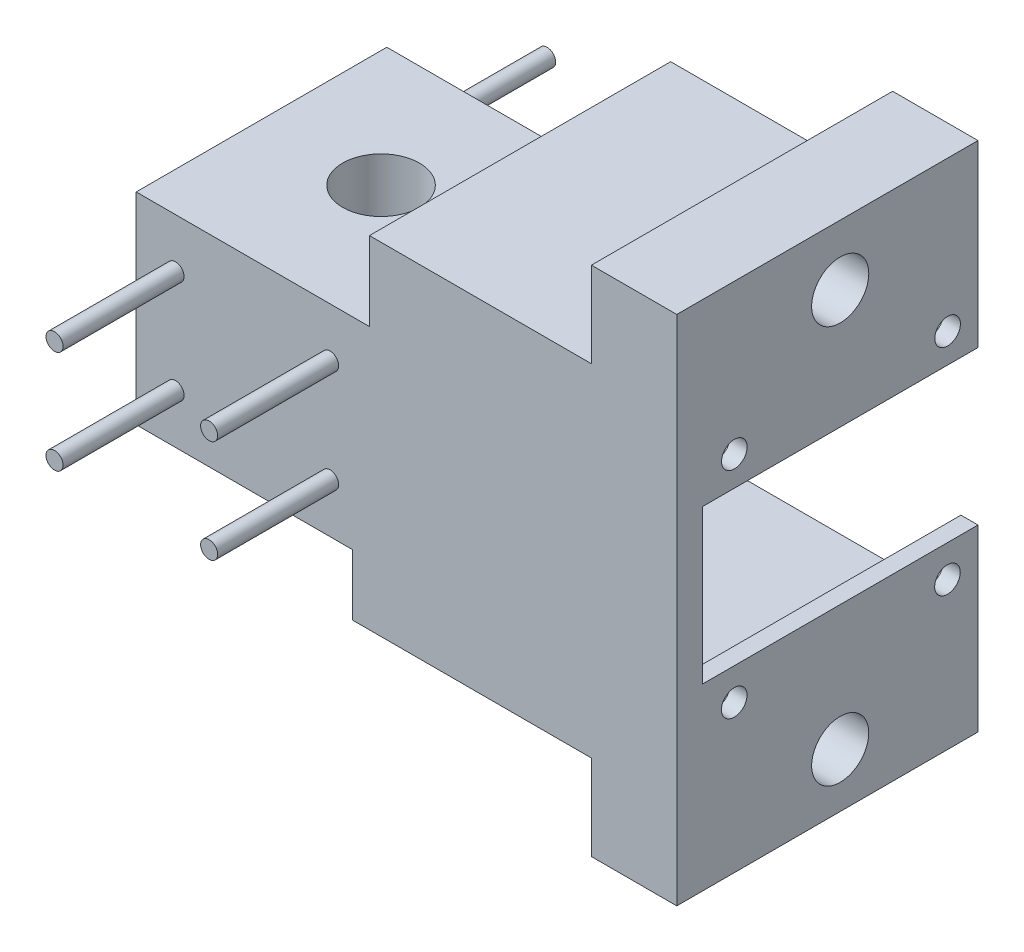
SolidWorks part; units mm, degrees
ref_plane "Front Plane" through (0, 0, 0) normal (0, 0, 1) x (1, 0, 0)
ref_plane "Top Plane" through (0, 0, 0) normal (0, 1, 0) x (1, 0, 0)
ref_plane "Right Plane" through (0, 0, 0) normal (1, 0, 0) x (0, 0, -1)
sketch "Sketch1" plane through (0, 0, -264.675) normal (0, 0, -1) x (-1, 0, 0)
  line L1 (-28.6765, -381.8964) -> (-63.3765, -381.8964)
  line L2 (-28.6765, -381.8964) -> (-28.6765, -411.8964)
  line L3 (-28.6765, -411.8964) -> (-63.3765, -411.8964)
  line L4 (-63.3765, -381.8964) -> (-63.3765, -411.8964)
extrude "Boss-Extrude1" add sketch "Sketch1" along normal up to surface (38.29 mm away)
sketch "Sketch2" plane through (0, 0, -264.675) normal (0, 0, 1) x (1, 0, 0)
  circle A0 centre (34.5265, -389.2464) radius 1.27
  circle A1 centre (34.5265, -404.5464) radius 1.27
  circle A2 centre (57.5265, -404.5464) radius 1.27
  circle A3 centre (57.5265, -389.2464) radius 1.27
  dimension "D1" = 2.54
extrude "Boss-Extrude2" add sketch "Sketch2" along a picked direction on the side of the normal blind 18 contours A0 | A3 | A2 | A1
sketch "Sketch4" plane through (0, -381.8964, 0) normal (0, 1, 0) x (1, 0, 0)
  circle A0 centre (46.0265, 283.7499) radius 5.715
  dimension "D1" = 11.43
extrude "Cut-Extrude1" cut sketch "Sketch4" against normal through all
sketch "Sketch5" plane through (0, -411.8964, 0) normal (0, -1, 0) x (1, 0, 0)
  circle A0 centre (46.4533, -275.536) radius 1.625
  circle A1 centre (54.2404, -284.1767) radius 1.625
  circle A2 centre (45.5996, -291.9638) radius 1.625
  circle A3 centre (37.8125, -283.3231) radius 1.625
  dimension "D1" = 3.25
extrude "Boss-Extrude4" add sketch "Sketch5" along normal blind 5
sketch "Sketch6" plane through (0, 0, -301.957) normal (0, 0, -1) x (-1, 0, 0)
  circle A0 centre (-57.5265, -389.2464) radius 1.27
  circle A1 centre (-34.5265, -389.2464) radius 1.27
  circle A2 centre (-34.5265, -404.5464) radius 1.27
  circle A3 centre (-57.5265, -404.5464) radius 1.27
  dimension "D1" = 2.54
extrude "Boss-Extrude5" add sketch "Sketch6" along normal up to surface (18 mm away)
sketch "Sketch8" plane through (63.3765, 0, 0) normal (1, 0, 0) x (0, 0, -1)
  line L1 (268.485, -420.9724) -> (264.675, -420.9724)
  line L2 (268.485, -420.9724) -> (268.485, -370.1724)
  line L3 (268.485, -370.1724) -> (264.675, -370.1724)
  line L4 (264.675, -420.9724) -> (264.675, -370.1724)
  line L5 (268.485, -420.9724) -> (264.675, -370.1724) construction
  line L6 (268.485, -370.1724) -> (264.675, -420.9724) construction
  point P0 (266.58, -395.5724)
  dimension "D1" = 50.8
  dimension "D2" = 3.81
extrude "Boss-Extrude6" add sketch "Sketch8" along normal blind 45.72
sketch "Sketch9" plane through (0, 0, -268.485) normal (0, 0, -1) x (-1, 0, 0)
  line L0 (-63.3765, -381.8964) -> (-63.3765, -370.1724) construction
  line L1 (-109.0965, -370.1724) -> (-63.3765, -370.1724)
  line L2 (-109.0965, -370.1724) -> (-109.0965, -372.7124)
  line L3 (-106.5565, -372.7124) -> (-63.3765, -372.7124)
  line L4 (-63.3765, -370.1724) -> (-63.3765, -372.7124)
  line L6 (-109.0965, -420.9724) -> (-63.3765, -420.9724)
  line L7 (-109.0965, -420.9724) -> (-109.0965, -418.4324)
  line L8 (-106.5565, -418.4324) -> (-63.3765, -418.4324)
  line L9 (-63.3765, -420.9724) -> (-63.3765, -418.4324)
  line L10 (-106.5565, -407.0024) -> (-106.5565, -418.4324)
  line L12 (-109.0965, -372.7124) -> (-109.0965, -384.1424)
  line L14 (-106.5565, -372.7124) -> (-106.5565, -384.1424)
  line L15 (-106.5565, -384.1424) -> (-109.0965, -384.1424)
  line L17 (-106.5565, -407.0024) -> (-109.0965, -407.0024)
  line L19 (-109.0965, -407.0024) -> (-109.0965, -418.4324)
  point P14 (-106.5565, -395.5724)
  dimension "D1" = 2.54
  dimension "D2" = 2.54
  dimension "D3" = 2.54
extrude "Boss-Extrude7" add sketch "Sketch9" along normal up to surface (41 mm away)
sketch "Sketch10" plane through (109.0965, 0, 0) normal (1, 0, 0) x (0, 0, -1)
  circle A0 centre (304.9635, -379.774) radius 1.905
  circle A1 centre (304.9419, -411.7524) radius 1.905
  circle A2 centre (273.239, -379.7524) radius 1.905
  circle A3 centre (273.2219, -411.7309) radius 1.905
  dimension "D1" = 3.81
  dimension "D2" = 31.7245
  dimension "D3" = 31.72
extrude "Cut-Extrude2" cut sketch "Sketch10" against normal up to next
sketch "Sketch11" plane through (0, -370.1724, 0) normal (0, 1, 0) x (1, 0, 0)
  line L0 (109.0965, 264.675) -> (63.3765, 264.675) construction
  line L1 (109.0965, 309.485) -> (96.3965, 309.485)
  line L2 (109.0965, 309.485) -> (109.0965, 264.675)
  line L3 (109.0965, 264.675) -> (96.3965, 264.675)
  line L4 (96.3965, 309.485) -> (96.3965, 264.675)
  dimension "D1" = 12.7
extrude "Boss-Extrude8" add sketch "Sketch11" along normal blind 12.7
sketch "Sketch12" plane through (0, -420.9724, 0) normal (0, -1, 0) x (1, 0, 0)
  line L0 (109.0965, -309.485) -> (63.3765, -309.485) construction
  line L1 (109.0965, -264.675) -> (96.3965, -264.675)
  line L2 (109.0965, -264.675) -> (109.0965, -309.485)
  line L3 (109.0965, -309.485) -> (96.3965, -309.485)
  line L4 (96.3965, -264.675) -> (96.3965, -309.485)
  dimension "D1" = 12.7
extrude "Boss-Extrude9" add sketch "Sketch12" along normal blind 12.7
sketch "Sketch13" plane through (109.0965, 0, 0) normal (1, 0, 0) x (0, 0, -1)
  line L0 (264.675, -357.4724) -> (309.485, -357.4724) construction
  line L1 (288.985, -395.7524) -> (288.985, -357.4724) construction
  circle A0 centre (288.985, -366.4724) radius 4.25
  circle A1 centre (288.985, -425.6544) radius 4.25
  dimension "D3" = 8.5
  dimension "D1" = 9
  dimension "D2" = 59.182
extrude "Cut-Extrude3" cut sketch "Sketch13" against normal blind 6.35
sketch "Sketch16" plane through (0, -411.8964, 0) normal (0, -1, 0) x (1, 0, 0)
  line L0 (28.6765, -301.957) -> (63.3765, -301.957) construction
  line L1 (63.3765, -264.675) -> (60.8765, -264.675)
  line L2 (63.3765, -264.675) -> (63.3765, -301.957)
  line L3 (63.3765, -301.957) -> (60.8765, -301.957)
  line L4 (60.8765, -264.675) -> (60.8765, -301.957)
  dimension "D1" = 2.5
sketch "Sketch17" plane through (0, 0, -268.485) normal (0, 0, -1) x (-1, 0, 0)
  line L0 (-63.3765, -418.4324) -> (-106.5565, -418.4324) construction
  line L1 (-63.3765, -372.7124) -> (-66.8124, -372.7124)
  line L2 (-63.3765, -372.7124) -> (-63.3765, -418.4324)
  line L3 (-63.3765, -418.4324) -> (-66.8124, -418.4324)
  line L4 (-66.8124, -372.7124) -> (-66.8124, -418.4324)
  dimension "D1" = 3.4359
extrude "Boss-Extrude12" add sketch "Sketch17" along normal up to surface (33.472 mm away) up to face at (57.5265, -405.8164, -301.957)
extrude "Boss-Extrude11" add sketch "Sketch16" along normal up to surface (9.0761 mm away) up to face at (79.8865, -420.9724, -287.08)
